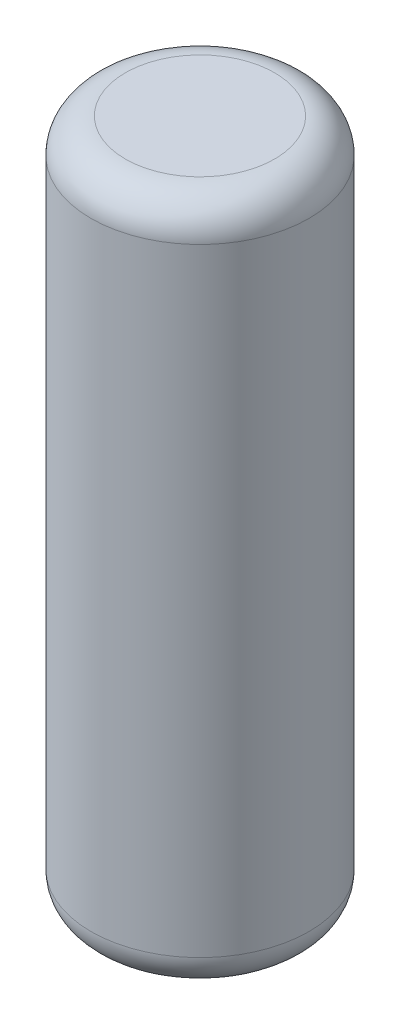
SolidWorks part; units mm, degrees
material "6061 Alloy"
ref_plane "Front" through (0, 0, 0) normal (0, 0, 1) x (1, 0, 0)
ref_plane "Top" through (0, 0, 0) normal (0, 1, 0) x (1, 0, 0)
ref_plane "Right" through (0, 0, 0) normal (1, 0, 0) x (0, 0, -1)
sketch "Sketch1" plane through (0, 0, 0) normal (0, 1, 0) x (1, 0, 0)
  circle A0 centre (0, 0) radius 1.5888
  dimension "D1" = 3.1775
extrude "Boss-Extrude1" add sketch "Sketch1" along normal mid plane 10
fillet "Fillet1" radius 0.5 2 edges at (0, -5, 1.5888) (0, 5, 1.5888)
